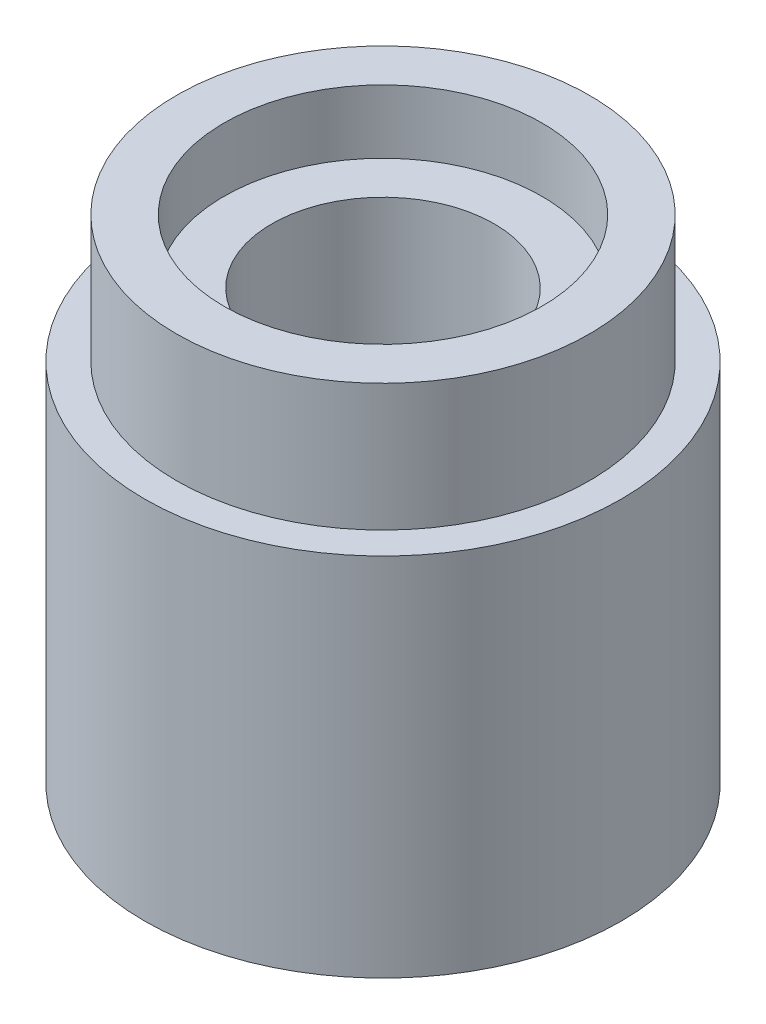
SolidWorks part; units mm, degrees
ref_plane "Front Plane" through (0, 0, 0) normal (0, 0, 1) x (1, 0, 0)
ref_plane "Top Plane" through (0, 0, 0) normal (0, 1, 0) x (1, 0, 0)
ref_plane "Right Plane" through (0, 0, 0) normal (1, 0, 0) x (0, 0, -1)
sketch "Sketch1" plane through (0, 0, 0) normal (0, 1, 0) x (1, 0, 0)
  circle A0 centre (0, 0) radius 3.75
extrude "Boss-Extrude1" add sketch "Sketch1" along normal blind 7.75
sketch "Sketch2" plane through (0, 7.75, 0) normal (0, 1, 0) x (1, 0, 0)
  circle A0 centre (0, 0) radius 2.5
  circle A1 centre (0, 0) radius 3.75
sketch "Sketch3" plane through (0, 7.75, 0) normal (0, 1, 0) x (1, 0, 0)
  circle A0 centre (0, 0) radius 3.25
  circle A1 centre (0, 0) radius 3.75
extrude "Cut-Extrude1" cut sketch "Sketch3" against normal blind 2
sketch "Sketch4" plane through (0, 7.75, 0) normal (0, 1, 0) x (1, 0, 0)
  circle A0 centre (0, 0) radius 1.75
extrude "Cut-Extrude2" cut sketch "Sketch4" against normal blind 7.25
sketch "Sketch5" plane through (0, 7.75, 0) normal (0, 1, 0) x (1, 0, 0)
  circle A0 centre (0, 0) radius 2.5
extrude "Cut-Extrude3" cut sketch "Sketch5" against normal blind 1
